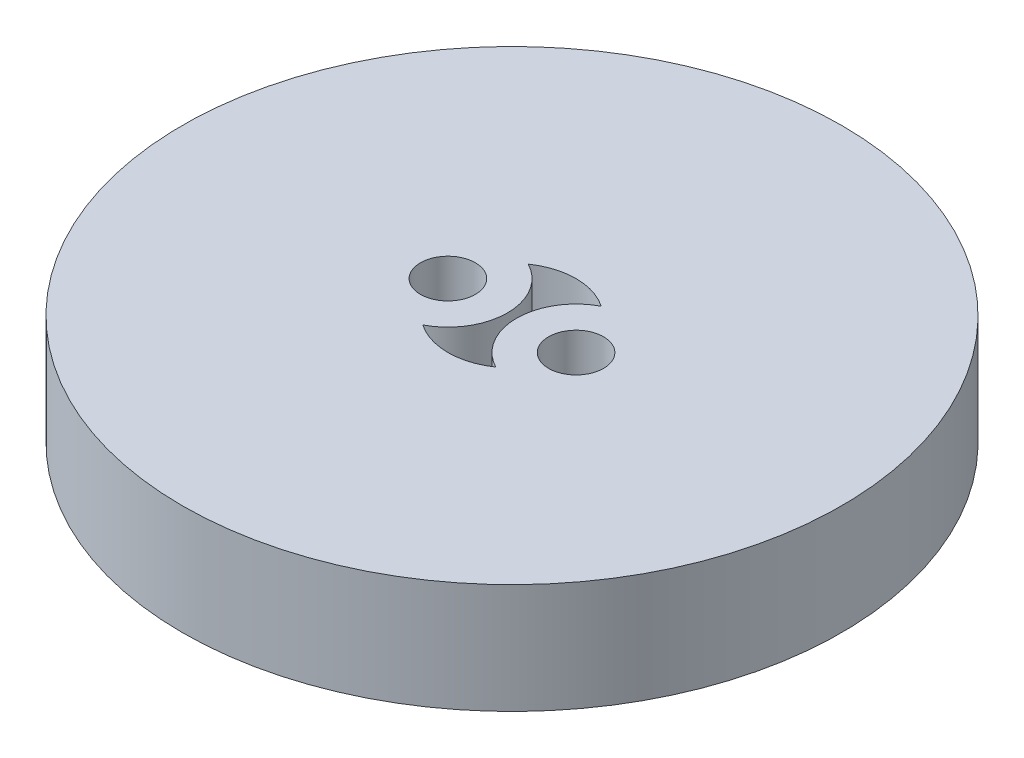
SolidWorks part; units mm, degrees
ref_plane "Plan de face" through (0, 0, 0) normal (0, 0, 1) x (1, 0, 0)
ref_plane "Plan de dessus" through (0, 0, 0) normal (0, 1, 0) x (1, 0, 0)
ref_plane "Plan de droite" through (0, 0, 0) normal (1, 0, 0) x (0, 0, -1)
sketch "Esquisse1" plane through (0, 0, 0) normal (0, 1, 0) x (1, 0, 0)
  line L0 (-3.5, 0) -> (3.5, 0) construction
  circle A0 centre (0, 0) radius 18
  circle A2 centre (-3.5, 0) radius 1.5
  circle A3 centre (3.5, 0) radius 1.5
  arc A4 (1.9911, 2.8785) -> (1.9911, -2.8785) centre (3.5, 0) ccw
  arc A5 (-1.9911, -2.8785) -> (-1.9911, 2.8785) centre (-3.5, 0) ccw
  arc A6 (-1.9911, -2.8785) -> (1.9911, -2.8785) centre (0, 0) ccw
  arc A9 (1.9911, 2.8785) -> (-1.9911, 2.8785) centre (0, 0) ccw
  circle A10 centre (-3.5, 0) radius 3.25 construction
  circle A11 centre (3.5, 0) radius 3.25 construction
  dimension "D1" = 36
  dimension "D2" = 6.5
  dimension "D3" = 6.5
  dimension "D4" = 7
  dimension "D5" = 3
  dimension "D6" = 3
  dimension "D7" = 3.5
  dimension "D8" = 3.5
  dimension "D9" = 3.25
  dimension "D10" = 3.25
  dimension "D11" = 3.5
extrude "Boss.-Extru.1" add sketch "Esquisse1" along normal blind 6
